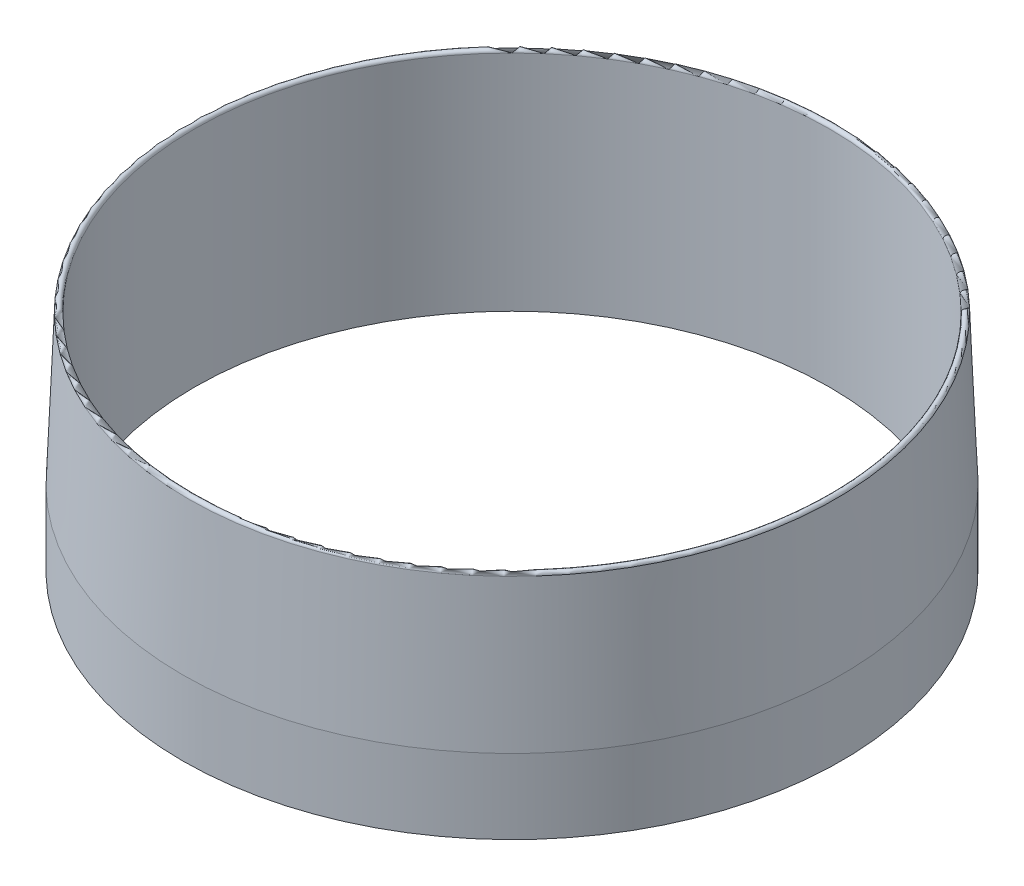
SolidWorks part; units mm, degrees
material "6061-T6 (SS)"
ref_plane "Front Plane" through (0, 0, 0) normal (0, 0, 1) x (1, 0, 0)
ref_plane "Top Plane" through (0, 0, 0) normal (0, 1, 0) x (1, 0, 0)
ref_plane "Right Plane" through (0, 0, 0) normal (1, 0, 0) x (0, 0, -1)
sketch "Sketch1" plane through (0, 0, 0) normal (0, 0, 1) x (1, 0, 0)
  line L0 (27.051, 0) -> (28.067, 0)
  line L1 (28.067, 0) -> (28.067, 6.35)
  line L2 (28.067, 6.35) -> (27.051, 31.75)
  line L3 (27.051, 31.75) -> (27.051, 0)
  dimension "D1" = 27.051
  dimension "D2" = 28.067
  dimension "D3" = 6.35
  dimension "D4" = 31.75
ref_axis "Axis1" through (0, -0.9525, 0) along (0, 1, 0)
revolve "Revolve1" add sketch "Sketch1" angle 360 about axis through (0, -0.9525, 0) along (0, 1, 0)
fillet "Fillet1" radius 0.254 1 edges at (0, 31.75, -27.051)
